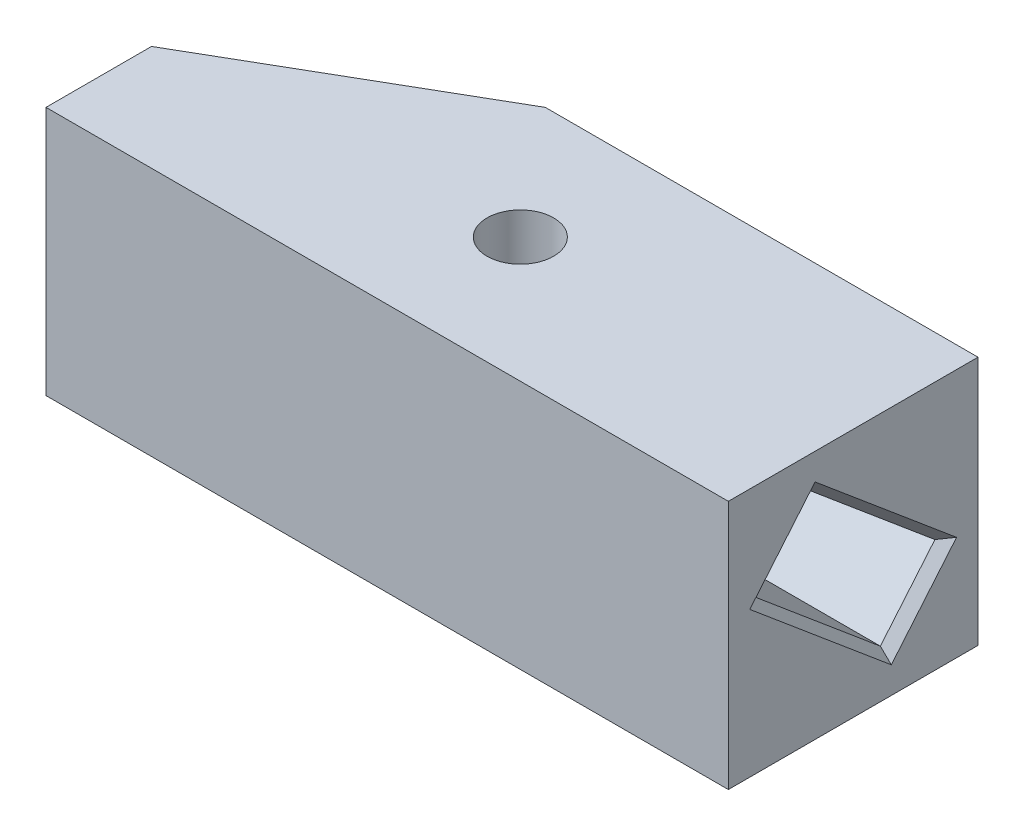
SolidWorks part; units mm, degrees
ref_plane "Спереди" through (0, 0, 0) normal (0, 0, 1) x (1, 0, 0)
ref_plane "Сверху" through (0, 0, 0) normal (0, 1, 0) x (1, 0, 0)
ref_plane "Справа" through (0, 0, 0) normal (1, 0, 0) x (0, 0, -1)
sketch "Эскиз1" plane through (0, 0, 0) normal (0, 1, 0) x (1, 0, 0)
  line L0 (-20, -15) -> (-35, -15)
  line L1 (-20, -15) -> (20, -15)
  line L2 (-35, -15) -> (-35, 15)
  line L3 (-20, 15) -> (20, 15)
  line L4 (20, -15) -> (20, 15)
  line L5 (-20, -15) -> (20, 15) construction
  line L6 (-20, 15) -> (20, -15) construction
  line L7 (-35, 15) -> (-20, 15)
  point P0 (0, 0)
  dimension "D1" = 40
  dimension "D2" = 30
  dimension "D3" = 15
extrude "Бобышка-Вытянуть1" add sketch "Эскиз1" along normal blind 30
sketch "Эскиз2" plane through (0, 30, 0) normal (0, 1, 0) x (1, 0, 0)
  line L0 (-20, -15) -> (-20, 15) construction
  circle A0 centre (-20, 0) radius 4
  dimension "D1" = 15
extrude "Вырез-Вытянуть1" cut sketch "Эскиз2" against normal through all
sketch "Эскиз5" plane through (20, 0, 0) normal (1, 0, 0) x (0, 0, -1)
  line L0 (0, 30) -> (0, 0) construction
  line L1 (-15, 30) -> (15, 0) construction
  line L2 (-15, 0) -> (15, 0) construction
  line L4 (4.4588, 4.601) -> (11.0153, 12.4147)
  line L5 (4.4588, 4.601) -> (-11.0153, 17.5853)
  line L6 (-11.0153, 17.5853) -> (-4.4588, 25.399)
  line L7 (11.0153, 12.4147) -> (-4.4588, 25.399)
  line L8 (4.4588, 4.601) -> (-4.4588, 25.399) construction
  line L9 (-11.0153, 17.5853) -> (11.0153, 12.4147) construction
  point P5 (0, 15)
  point P6 (0, 15)
  dimension "D1" = 20.2
  dimension "D2" = 10.2
  dimension "D3" = 40
extrude "Вырез-Вытянуть4" cut sketch "Эскиз5" against normal blind 30
sketch "Sketch1" plane through (-35, 0, 0) normal (-1, 0, 0) x (0, 0, 1)
  line L0 (0, 30) -> (0, 0) construction
  line L1 (-15, 30) -> (15, 30) construction
  line L3 (-15, 0) -> (15, 0)
  line L4 (-15, 0) -> (-15, 30)
  line L5 (-15, 30) -> (15, 30)
  line L6 (15, 0) -> (15, 30)
  line L7 (-15, 0) -> (15, 30) construction
  line L8 (-15, 30) -> (15, 0) construction
  point P5 (0, 15)
extrude "Boss-Extrude1" add sketch "Sketch1" along normal blind 27
chamfer "Chamfer1" distance 30 angle 30 1 edges at (-62, 15, -15)
chamfer "Chamfer2" distance 1 angle 50 4 edges at (20, 8.5078, -7.737) (20, 18.9068, -3.2782) (20, 21.4922, 7.737) (20, 11.0932, 3.2782)
